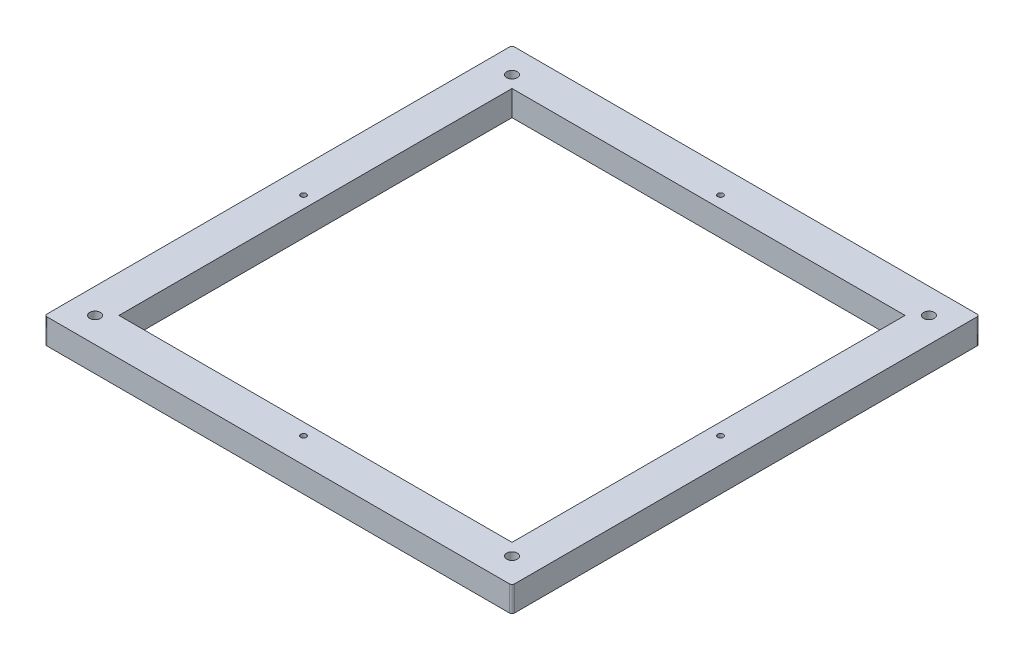
SolidWorks part; units mm, degrees
ref_plane "Plan de face" through (0, 0, 0) normal (0, 0, 1) x (1, 0, 0)
ref_plane "Plan de dessus" through (0, 0, 0) normal (0, 1, 0) x (1, 0, 0)
ref_plane "Plan de droite" through (0, 0, 0) normal (1, 0, 0) x (0, 0, -1)
sketch "Esquisse2" plane through (0, 0, 0) normal (0, 1, 0) x (1, 0, 0)
  line L1 (-92.5, 92.5) -> (92.5, 92.5)
  line L2 (-92.5, 92.5) -> (-92.5, -92.5)
  line L3 (-92.5, -92.5) -> (92.5, -92.5)
  line L4 (92.5, 92.5) -> (92.5, -92.5)
  line L5 (-77.77, 77.77) -> (77.77, 77.77)
  line L6 (-77.77, 77.77) -> (-77.77, -77.77)
  line L7 (-77.77, -77.77) -> (77.77, -77.77)
  line L8 (77.77, 77.77) -> (77.77, -77.77)
  circle A0 centre (-82.5, 82.5) radius 1.1
  circle A1 centre (82.5, 82.5) radius 1.1
  circle A2 centre (0, 82.5) radius 1.1
  circle A3 centre (-82.5, 0) radius 1.1
  circle A4 centre (82.5, 0) radius 1.1
  circle A5 centre (82.5, -82.5) radius 1.1
  circle A6 centre (0, -82.5) radius 1.1
  circle A7 centre (-82.5, -82.5) radius 1.1
  dimension "D11" = 2.2
  dimension "D1" = 185
  dimension "D2" = 185
  dimension "D3" = 92.5
  dimension "D4" = 92.5
  dimension "D5" = 14.73
  dimension "D6" = 14.73
  dimension "D7" = 14.73
  dimension "D8" = 14.73
  dimension "D9" = 155.54
  dimension "D10" = 155.54
  dimension "D12" = 10
  dimension "D13" = 10
  dimension "D14" = 10
  dimension "D15" = 10
  dimension "D16" = 82.5
  dimension "D17" = 82.5
extrude "Boss.-Extru.1" add sketch "Esquisse2" against normal blind 10
fillet "Congé1" radius 1 4 edges at (-92.5, -5, -92.5) (92.5, -5, -92.5) (92.5, -5, 92.5) (-92.5, -5, 92.5)
sketch "Esquisse3" plane through (0, 0, 0) normal (0, 1, 0) x (1, 0, 0)
  circle A0 centre (-82.5, -82.5) radius 2.1
  circle A2 centre (-82.5, 82.5) radius 2.1
  circle A3 centre (-82.5, 82.5) radius 1.1 construction
  circle A4 centre (82.5, 82.5) radius 2.1
  circle A5 centre (82.5, 82.5) radius 1.1 construction
  circle A6 centre (82.5, -82.5) radius 2.1
  circle A8 centre (82.5, -82.5) radius 1.1 construction
  circle A9 centre (-82.5, -82.5) radius 1.1 construction
  point P16 (0, 0)
  point P17 (0, 0)
  dimension "D1" = 4.2
extrude "Enlèv. mat.-Extru.1" cut sketch "Esquisse3" against normal blind 8
